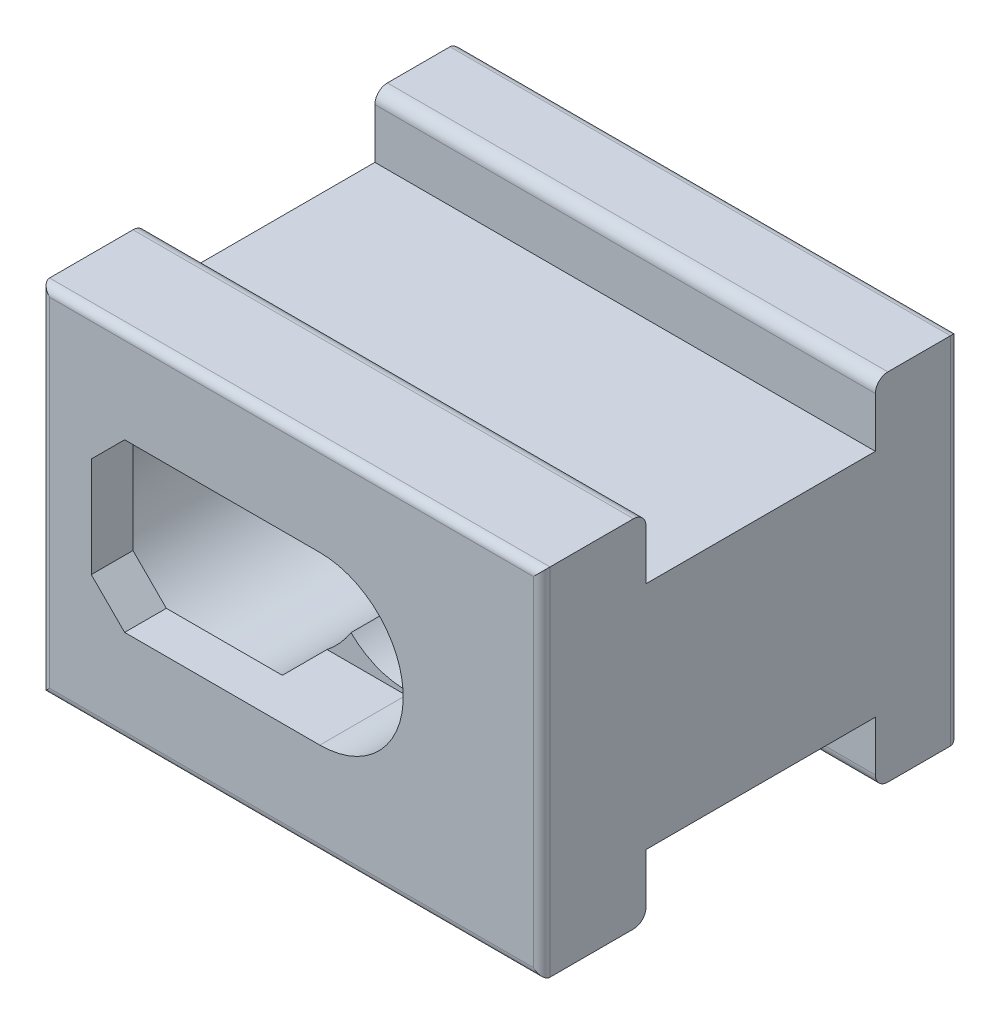
SolidWorks part; units mm, degrees
ref_plane "Plan de face" through (0, 0, 0) normal (0, 0, 1) x (1, 0, 0)
ref_plane "Plan de dessus" through (0, 0, 0) normal (0, 1, 0) x (1, 0, 0)
ref_plane "Plan de droite" through (0, 0, 0) normal (1, 0, 0) x (0, 0, -1)
sketch "Esquisse1" plane through (0, 0, 0) normal (0, 0, 1) x (1, 0, 0)
  line L1 (-60, 42.6) -> (60, 42.6)
  line L2 (-60, 42.6) -> (-60, -42.6)
  line L3 (-60, -42.6) -> (60, -42.6)
  line L4 (60, 42.6) -> (60, -42.6)
  line L5 (-60, 42.6) -> (60, -42.6) construction
  line L6 (-60, -42.6) -> (60, 42.6) construction
  point P0 (0, 0)
  dimension "D1" = 85.2
  dimension "D2" = 120
extrude "Boss.-Extru.1" add sketch "Esquisse1" along normal blind 100
sketch "Esquisse2" plane through (-60, 0, 0) normal (-1, 0, 0) x (0, 0, 1)
  line L0 (0, 0) -> (100, 0) construction
  line L1 (100, 42.6) -> (100, -42.6) construction
  line L2 (50, 0) -> (50, 42.6) construction
  line L3 (100, 42.6) -> (0, 42.6) construction
  line L4 (50, 42.6) -> (50, -42.6) construction
  line L5 (100, -42.6) -> (0, -42.6) construction
  line L6 (0, 42.6) -> (0, -42.6) construction
  line L7 (75, 42.6) -> (20, 42.6)
  line L8 (75, 42.6) -> (75, 27.6)
  line L9 (75, 27.6) -> (20, 27.6)
  line L10 (20, 42.6) -> (20, 27.6)
  line L12 (20, -42.6) -> (75, -42.6)
  line L13 (20, -42.6) -> (20, -27.6)
  line L14 (20, -27.6) -> (75, -27.6)
  line L15 (75, -42.6) -> (75, -27.6)
  dimension "D1" = 25
  dimension "D2" = 20
  dimension "D3" = 15
  dimension "D4" = 20
  dimension "D5" = 25
  dimension "D6" = 15
  dimension "D7" = 55
extrude "Enlèv. mat.-Extru.1" cut sketch "Esquisse2" against normal through all
fillet "Congé1" radius 3 4 edges at (0, -42.6, 75) (0, -42.6, 20) (0, 42.6, 75) (0, 42.6, 20)
fillet "Congé2" radius 2 4 edges at (60, 0, 0) (0, -42.6, 0) (-60, 0, 0) (0, 42.6, 0)
fillet "Congé3" radius 2 4 edges at (0, -42.6, 100) (-60, 0, 100) (0, 42.6, 100) (60, 0, 100)
sketch "Esquisse3" plane through (0, 0, 0) normal (0, 0, -1) x (-1, 0, 0)
  line L1 (-0.1116, 0) -> (20.6653, 0) construction
  line L2 (60, 42.6) -> (60, -42.6) construction
  circle A2 centre (28, 0) radius 25.5
  dimension "D1" = 51
  dimension "D2" = 32
extrude "Enlèv. mat.-Extru.2" cut sketch "Esquisse3" against normal blind 90
fillet "Congé4" radius 1 1 edges at (-53.5, 0, 0)
sketch "Esquisse5" plane through (0, 0, 100) normal (0, 0, 1) x (1, 0, 0)
  line L0 (-60, -42.6) -> (-60, 42.6) construction
  line L1 (-28, 0) -> (-48, 0) construction
  line L2 (-28, 0) -> (-28, 20) construction
  line L3 (-28, 0) -> (-28, -20) construction
  line L4 (-48, 0) -> (-48, 12)
  line L5 (-48, 0) -> (-48, -12)
  line L6 (-28, 20) -> (-40, 20)
  line L7 (-40, 20) -> (-48, 12)
  line L8 (-28, -20) -> (-40, -20)
  line L9 (-48, -12) -> (-40, -20)
  line L10 (-28, 20) -> (6.8, 20)
  line L11 (6.8, -20) -> (-28, -20)
  arc A1 (6.8, 20) -> (6.8, -20) centre (6.8, 0) cw
  point P0 (-28, 0)
  dimension "D1" = 32
  dimension "D2" = 12
extrude "Enlèv. mat.-Extru.3" cut sketch "Esquisse5" against normal blind 20.7 contours L11 L8 L9 L5 L4 L7 L6 L10 A1
sketch "Esquisse6" plane through (0, 0, 79.3) normal (0, 0, 1) x (1, 0, 0)
  line L0 (6.8, -20) -> (6.8, 20) construction
  arc A0 (6.8, -20) -> (6.8, 20) centre (6.8, 0) ccw construction
  circle A1 centre (6.8, 0) radius 19
  point P6 (6.8, 0)
  dimension "D1" = 38
extrude "Enlèv. mat.-Extru.5" cut sketch "Esquisse6" against normal blind 85
